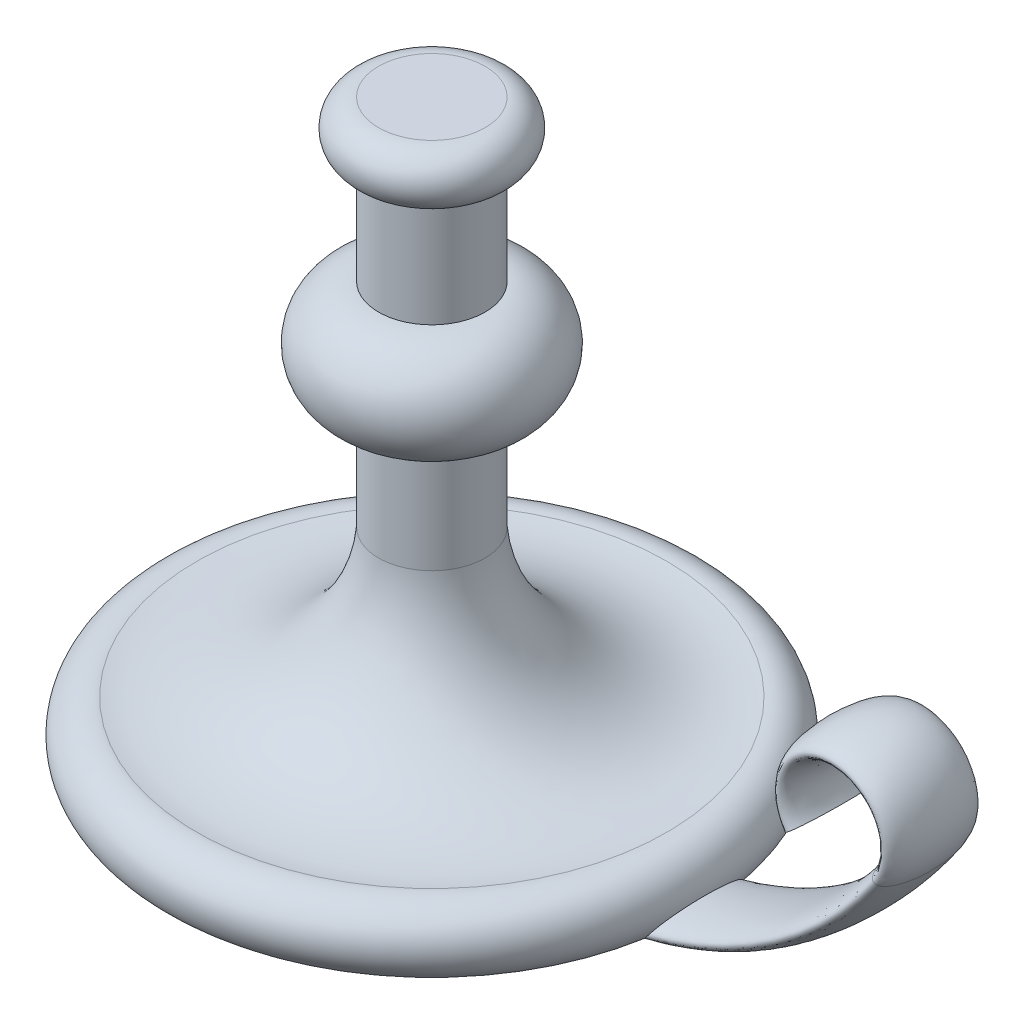
SolidWorks part; units mm, degrees
ref_plane "Front Plane" through (0, 0, 0) normal (0, 0, 1) x (1, 0, 0)
ref_plane "Top Plane" through (0, 0, 0) normal (0, 1, 0) x (1, 0, 0)
ref_plane "Right Plane" through (0, 0, 0) normal (1, 0, 0) x (0, 0, -1)
sketch "Sketch1" plane through (0, 0, 0) normal (0, 0, 1) x (1, 0, 0)
  line L0 (0, 0) -> (0, 5588)
  line L1 (0, 0) -> (2286, 0)
  line L2 (0, 5588) -> (508, 5588)
  line L3 (508, 5080) -> (508, 4064)
  line L4 (508, 3048) -> (508, 2032)
  arc A0 (508, 5588) -> (508, 5080) centre (508, 5334) cw
  arc A1 (508, 4064) -> (508, 3048) centre (508, 3556) cw
  arc A2 (2286, 0) -> (2241.5358, 631.8711) centre (2286, 317.5) ccw
  arc A3 (2241.5358, 631.8711) -> (508, 2032) centre (2028.1076, 2140.8523) cw
  dimension "D4" = 254
  dimension "D5" = 508
  dimension "D8" = 317.5
  dimension "D9" = 1524
  dimension "D1" = 508
  dimension "D2" = 5588
  dimension "D3" = 2286
  dimension "D6" = 1016
  dimension "D7" = 2032
revolve "Revolve1" add sketch "Sketch1" angle 360 about L0
sketch "Sketch4" plane through (0, 0, 0) normal (0, 0, 1) x (1, 0, 0)
  line L0 (0, -3.4766) -> (1524, -3.4766)
  line L1 (0, 4165.6) -> (0, 2336.8) construction
  arc A0 (1524, -3.4766) -> (4663.2386, 1647.5234) centre (1524, 3806.5234) ccw
  arc A1 (4663.2386, 1647.5234) -> (3826.1083, 1647.5234) centre (4244.6735, 1935.3901) ccw
  dimension "D1" = 1524
  dimension "D2" = 3810
  dimension "D4" = 508
  dimension "D3" = 1651
sketch "Sketch9" plane through (0, 0, 0) normal (1, 0, 0) x (0, 0, -1)
  ellipse E0 centre (0, 0) end of major axis (-444.5, 0) minor radius 127
  point P1 (0, 0)
  point P7 (0, 0)
  point P8 (-2831.0704, 3804.7323)
  point P9 (0, 0)
  dimension "D1" = 254
  dimension "D2" = 889
sweep "Sweep1" add profiles "Sketch9" path "Sketch4"
